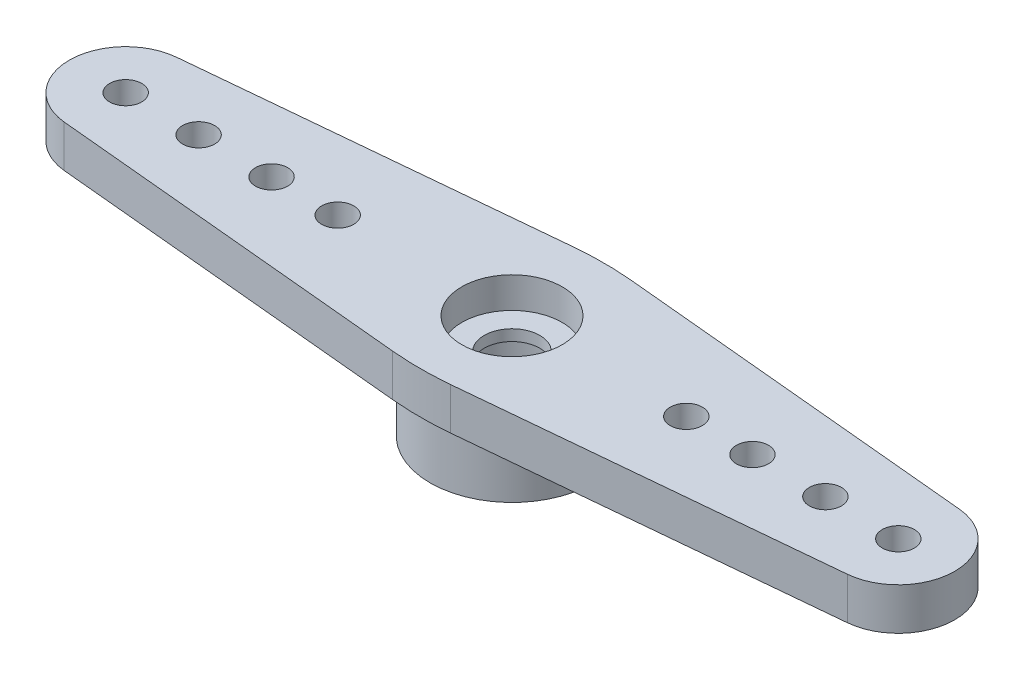
SolidWorks part; units mm, degrees
ref_plane "Front Plane" through (0, 0, 0) normal (0, 0, 1) x (1, 0, 0)
ref_plane "Top Plane" through (0, 0, 0) normal (0, 1, 0) x (1, 0, 0)
ref_plane "Right Plane" through (0, 0, 0) normal (1, 0, 0) x (0, 0, -1)
sketch "Sketch1" plane through (0, 0, 0) normal (0, 1, 0) x (1, 0, 0)
  circle A0 centre (0, 0) radius 3.3655
  circle A1 centre (0, 0) radius 2.2352
  dimension "D1" = 6.731
  dimension "D2" = 4.4704
extrude "Boss-Extrude1" add sketch "Sketch1" along normal blind 2.54
sketch "Sketch2" plane through (0, 2.54, 0) normal (0, 1, 0) x (1, 0, 0)
  line L0 (0, 0) -> (50000, 0) construction
  line L1 (0, 0) -> (0, 50000) construction
  line L2 (0, 3.8227) -> (16.0923, 2.3075)
  line L3 (0, -3.8227) -> (16.0923, -2.3075)
  line L4 (0, -3.8227) -> (-16.0923, -2.3075)
  line L5 (0, 3.8227) -> (-16.0923, 2.3075)
  circle A0 centre (15.875, 0) radius 0.6604
  circle A1 centre (12.8778, 0) radius 0.6604
  circle A2 centre (9.8806, 0) radius 0.6604
  circle A3 centre (7.1628, 0) radius 0.6604
  circle A4 centre (15.875, 0) radius 2.3178
  circle A5 centre (0, 0) radius 3.8227
  circle A6 centre (-15.875, 0) radius 2.3178
  circle A7 centre (-7.1628, 0) radius 0.6604
  circle A8 centre (-9.8806, 0) radius 0.6604
  circle A9 centre (-12.8778, 0) radius 0.6604
  circle A10 centre (-15.875, 0) radius 0.6604
  circle A11 centre (0, 0) radius 1.143
  circle M1 centre (0, 0) radius 3.3655
  circle M2 centre (0, 0) radius 2.2352
  dimension "D1" = 1.3208
  dimension "D6" = 4.6355
  dimension "D7" = 7.6454
  dimension "D8" = 2.286
  dimension "D2" = 15.875
  dimension "D3" = 2.9972
  dimension "D4" = 5.9944
  dimension "D5" = 8.7122
extrude "Boss-Extrude2" add sketch "Sketch2" along normal blind 1.7272 contours L5 A6 L4 A5 A8 A7 A9 | A6 A10 | A5 L3 A4 L2 A1 A2 A3 | A4 A0 | M1 M2 | L3 A5 L2 L5 L4 M1 | A11 M2
fillet "Fillet1" radius 12.7 2 edges at (0, 3.4036, -3.8227) (0, 3.4036, 3.8227)
sketch "Sketch3" plane through (0, 4.2672, 0) normal (0, 1, 0) x (1, 0, 0)
  circle A0 centre (0, 0) radius 2.0638
  circle M17 centre (0, 0) radius 1.143
  dimension "D1" = 4.1275
extrude "Cut-Extrude1" cut sketch "Sketch3" against normal blind 1.27 contours A0 M17
sketch "Sketch4" plane through (0, 4.2672, 0) normal (0, 1, 0) x (1, 0, 0)
  circle A0 centre (-15.875, 0) radius 0.6604 construction
  circle A1 centre (-12.8778, 0) radius 0.6604 construction
  circle A2 centre (-9.8806, 0) radius 0.6604 construction
  circle A3 centre (-7.1628, 0) radius 0.6604 construction
  circle A4 centre (15.875, 0) radius 0.6604 construction
  circle A5 centre (12.8778, 0) radius 0.6604 construction
  circle A6 centre (9.8806, 0) radius 0.6604 construction
  circle A7 centre (7.1628, 0) radius 0.6604 construction
  circle A9 centre (-15.875, 0) radius 0.6604
  circle A10 centre (-12.8778, 0) radius 0.6604
  circle A11 centre (-9.8806, 0) radius 0.6604
  circle A12 centre (-7.1628, 0) radius 0.6604
  circle A13 centre (15.875, 0) radius 0.6604
  circle A14 centre (12.8778, 0) radius 0.6604
  circle A15 centre (9.8806, 0) radius 0.6604
  circle A16 centre (7.1628, 0) radius 0.6604
  circle A18 centre (0, 0) radius 1.143 construction
  circle A19 centre (0, 0) radius 1.143
sketch "Sketch5" plane through (0, 4.2672, 0) normal (0, 1, 0) x (1, 0, 0)
  line L0 (1.1905, -3.7106) -> (16.0923, -2.3075) construction
  line L1 (-1.1905, -3.7106) -> (-16.0923, -2.3075) construction
  line L2 (-1.1905, 3.7106) -> (-16.0923, 2.3075) construction
  line L3 (1.1905, 3.7106) -> (16.0923, 2.3075) construction
  line L4 (1.1905, -3.7106) -> (16.0923, -2.3075)
  line L5 (-1.1905, -3.7106) -> (-16.0923, -2.3075)
  line L6 (-1.1905, 3.7106) -> (-16.0923, 2.3075)
  line L7 (1.1905, 3.7106) -> (16.0923, 2.3075)
  arc A0 (16.0923, -2.3075) -> (16.0923, 2.3075) centre (15.875, 0) ccw construction
  arc A1 (-1.1905, -3.7106) -> (1.1905, -3.7106) centre (0, 8.9335) ccw construction
  arc A2 (-16.0923, 2.3075) -> (-16.0923, -2.3075) centre (-15.875, 0) ccw construction
  arc A3 (1.1905, 3.7106) -> (-1.1905, 3.7106) centre (0, -8.9335) ccw construction
  arc A4 (16.0923, -2.3075) -> (16.0923, 2.3075) centre (15.875, 0) ccw
  arc A5 (-1.1905, -3.7106) -> (1.1905, -3.7106) centre (0, 8.9335) ccw
  arc A6 (-16.0923, 2.3075) -> (-16.0923, -2.3075) centre (-15.875, 0) ccw
  arc A7 (1.1905, 3.7106) -> (-1.1905, 3.7106) centre (0, -8.9335) ccw
